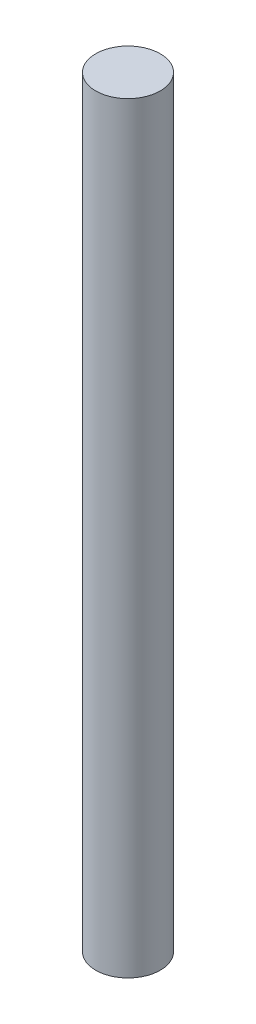
SolidWorks part; units mm, degrees
material "Maple"
ref_plane "Front Plane" through (0, 0, 0) normal (0, 0, 1) x (1, 0, 0)
ref_plane "Top Plane" through (0, 0, 0) normal (0, 1, 0) x (1, 0, 0)
ref_plane "Right Plane" through (0, 0, 0) normal (1, 0, 0) x (0, 0, -1)
sketch "Sketch1" plane through (0, 0, 0) normal (0, 1, 0) x (1, 0, 0)
  circle A0 centre (0, 0) radius 6.35
  dimension "D1" = 12.7
extrude "Boss-Extrude1" add sketch "Sketch1" along normal blind 150
